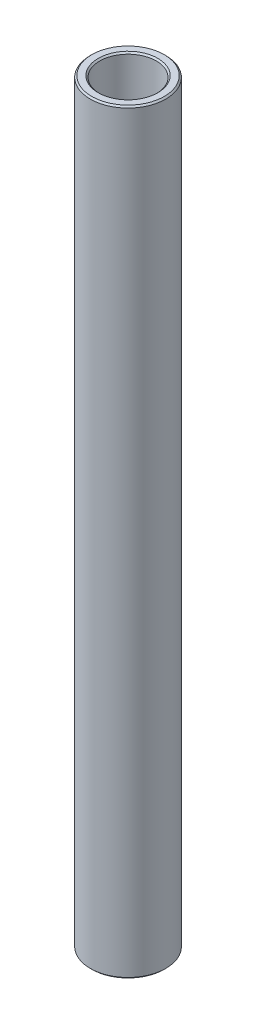
SolidWorks part; units mm, degrees
ref_plane "Front Plane" through (0, 0, 0) normal (0, 0, 1) x (1, 0, 0)
ref_plane "Top Plane" through (0, 0, 0) normal (0, 1, 0) x (1, 0, 0)
ref_plane "Right Plane" through (0, 0, 0) normal (1, 0, 0) x (0, 0, -1)
sketch "Sketch1" plane through (0, 0, 0) normal (0, 0, 1) x (1, 0, 0)
  line L0 (4.7625, 70.6437) -> (4.7625, 197.8308)
  line L1 (4.7625, 197.8308) -> (6.35, 197.8308)
  line L2 (6.35, 197.8308) -> (6.35, 70.6437)
  line L3 (6.35, 70.6437) -> (4.7625, 70.6437)
  line L4 (-10.0875, 79.3749) -> (-120.0875, 79.3749) construction
  line L6 (0, 61.1187) -> (0, 207.3558) construction
  dimension "D1" = 9.525
  dimension "D2" = 9.525
  dimension "D3" = 12.7
  dimension "D4" = 9.525
revolve "Revolve1" add sketch "Sketch1" angle 360 about L6
chamfer "Chamfer1" distance 0.254 angle 45 4 edges at (6.35, 197.8308, 0) (4.7625, 197.8308, 0) (4.7625, 70.6437, 0) (6.35, 70.6437, 0)
equation "\"D4@Sketch1\"=\"D1@Sketch1\""
